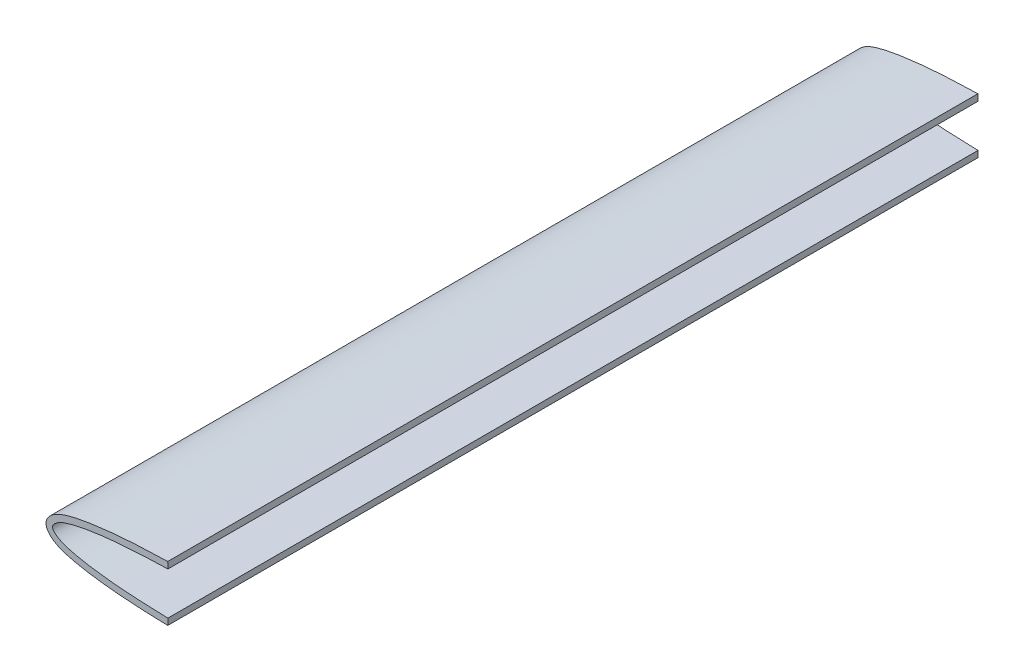
SolidWorks part; units mm, degrees
material "Balsa"
ref_plane "Front Plane" through (0, 0, 0) normal (0, 0, 1) x (1, 0, 0)
ref_plane "Top Plane" through (0, 0, 0) normal (0, 1, 0) x (1, 0, 0)
ref_plane "Right Plane" through (0, 0, 0) normal (1, 0, 0) x (0, 0, -1)
sketch "Sketch1" plane through (0, 0, 0) normal (0, 0, 1) x (1, 0, 0)
  line L0 (40.894, 7.5344) -> (40.8429, 9.8199)
  line L2 (40.8429, -9.8199) -> (40.894, -7.5344)
  spline S0 degree 3 poles (40.894, 7.5344) (39.8081, 7.5102) (37.2205, 7.4418) (33.2049, 7.2882) (28.927, 7.0643) (24.8872, 6.7834) (21.1028, 6.4501) (17.5912, 6.0616) (14.3671, 5.6253) (11.443, 5.1524) (8.831, 4.6451) (6.5398, 4.105) (4.5802, 3.5141) (2.9563, 2.8613) (1.6831, 2.141) (0.7676, 1.3889) (0.1958, 0.6995) (-0.0801, 0) (0.1958, -0.6995) (0.7676, -1.3889) (1.6831, -2.141) (2.9563, -2.8613) (4.5802, -3.5141) (6.5398, -4.105) (8.831, -4.6451) (11.443, -5.1524) (14.3671, -5.6253) (17.5912, -6.0616) (21.1028, -6.4501) (24.8872, -6.7834) (28.927, -7.0643) (33.2049, -7.2882) (37.2205, -7.4418) (39.8081, -7.5102) (40.894, -7.5344) knots 0.375678 0.375678 0.375678 0.375678 0.385183 0.398331 0.410845 0.422673 0.433769 0.44409 0.453589 0.46224 0.47001 0.476871 0.482833 0.487909 0.492155 0.495592 0.498196 0.5 0.501804 0.504408 0.507845 0.512091 0.517167 0.523129 0.52999 0.53776 0.546411 0.55591 0.566231 0.577327 0.589155 0.601669 0.614817 0.624322 0.624322 0.624322 0.624322
  spline S1 degree 1 poles (40.8429, 9.8199) (40.8429, -9.8199) knots 0 0 1 1 construction
  spline S2 degree 3 poles (40.8429, 9.8199) (39.056, 9.7799) (35.4835, 9.6749) (30.122, 9.4298) (24.7547, 9.0765) (20.2776, 8.669) (16.694, 8.2483) (14.0089, 7.8797) (11.3224, 7.4507) (8.6313, 6.9407) (6.3747, 6.4223) (4.5382, 5.8926) (3.1476, 5.4124) (1.9628, 4.9011) (1.0046, 4.3824) (0.2888, 3.9257) (-0.4218, 3.3744) (-0.9689, 2.8578) (-1.442, 2.2991) (-1.7805, 1.7928) (-2.0533, 1.2557) (-2.2405, 0.6197) (-2.3087, 0) (-2.2405, -0.6197) (-2.0533, -1.2557) (-1.7805, -1.7928) (-1.442, -2.2991) (-0.9689, -2.8578) (-0.4218, -3.3744) (0.2888, -3.9257) (1.0046, -4.3824) (1.9628, -4.9011) (3.1476, -5.4124) (4.5382, -5.8926) (6.3747, -6.4223) (8.6313, -6.9407) (11.3224, -7.4507) (14.0089, -7.8797) (16.694, -8.2483) (20.2776, -8.669) (24.7547, -9.0765) (30.122, -9.4298) (35.4835, -9.6749) (39.056, -9.7799) (40.8429, -9.8199) knots 0.375678 0.375678 0.375678 0.375678 0.391218 0.406758 0.422298 0.437839 0.445609 0.453379 0.461149 0.468919 0.47669 0.480575 0.48446 0.488345 0.490287 0.49223 0.494172 0.496115 0.497086 0.498057 0.499029 0.499514 0.5 0.500486 0.500971 0.501943 0.502914 0.503885 0.505828 0.50777 0.509713 0.511655 0.51554 0.519425 0.52331 0.531081 0.538851 0.546621 0.554391 0.562161 0.577702 0.593242 0.608782 0.624322 0.624322 0.624322 0.624322
  point P7 (40.894, 0)
  dimension "D1" = 2.286
extrude "Boss-Extrude1" add sketch "Sketch1" along normal blind 287.02
